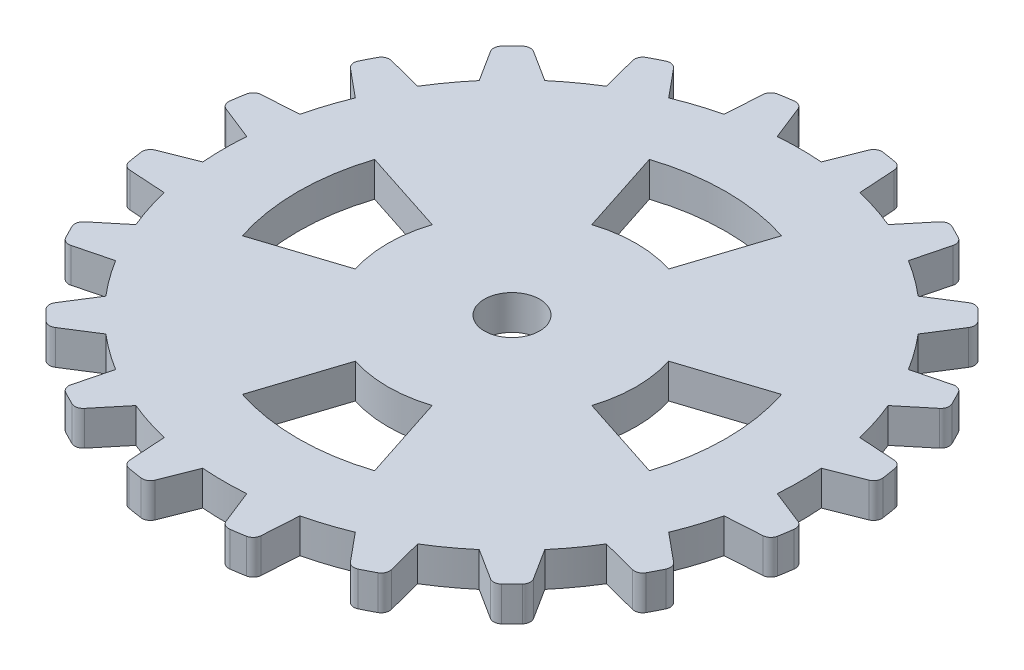
SolidWorks part; units mm, degrees
ref_plane "Front Plane" through (0, 0, 0) normal (0, 0, 1) x (1, 0, 0)
ref_plane "Top Plane" through (0, 0, 0) normal (0, 1, 0) x (1, 0, 0)
ref_plane "Right Plane" through (0, 0, 0) normal (1, 0, 0) x (0, 0, -1)
sketch "Sketch1" plane through (0, 0, 0) normal (0, 1, 0) x (1, 0, 0)
  line L0 (0, 0) -> (0, 28.8903) construction
  line L1 (-2.7439, 23.715) -> (0, 0)
  line L2 (2.7439, 23.715) -> (0, 0)
  line L3 (-2.7439, 23.715) -> (-1.5946, 20.8122)
  line L4 (2.7439, 23.715) -> (1.5946, 20.8122)
  line L5 (4.7187, 23.4022) -> (4.9148, 20.2864)
  line L6 (9.938, 21.7064) -> (7.9479, 19.3009)
  line L7 (11.7195, 20.7987) -> (10.943, 17.7748)
  line L8 (16.1592, 17.573) -> (13.5232, 15.9002)
  line L9 (17.573, 16.1592) -> (15.9002, 13.5232)
  line L10 (20.7987, 11.7195) -> (17.7748, 10.943)
  line L11 (21.7064, 9.938) -> (19.3009, 7.9479)
  line L12 (23.4022, 4.7187) -> (20.2864, 4.9148)
  line L13 (23.715, 2.7439) -> (20.8122, 1.5946)
  line L14 (23.715, -2.7439) -> (20.8122, -1.5946)
  line L15 (23.4022, -4.7187) -> (20.2864, -4.9148)
  line L16 (21.7064, -9.938) -> (19.3009, -7.9479)
  line L17 (20.7987, -11.7195) -> (17.7748, -10.943)
  line L18 (17.573, -16.1592) -> (15.9002, -13.5232)
  line L19 (16.1592, -17.573) -> (13.5232, -15.9002)
  line L20 (11.7195, -20.7987) -> (10.943, -17.7748)
  line L21 (9.938, -21.7064) -> (7.9479, -19.3009)
  line L22 (4.7187, -23.4022) -> (4.9148, -20.2864)
  line L23 (2.7439, -23.715) -> (1.5946, -20.8122)
  line L24 (-2.7439, -23.715) -> (-1.5946, -20.8122)
  line L25 (-4.7187, -23.4022) -> (-4.9148, -20.2864)
  line L26 (-9.938, -21.7064) -> (-7.9479, -19.3009)
  line L27 (-11.7195, -20.7987) -> (-10.943, -17.7748)
  line L28 (-16.1592, -17.573) -> (-13.5232, -15.9002)
  line L29 (-17.573, -16.1592) -> (-15.9002, -13.5232)
  line L30 (-20.7987, -11.7195) -> (-17.7748, -10.943)
  line L31 (-21.7064, -9.938) -> (-19.3009, -7.9479)
  line L32 (-23.4022, -4.7187) -> (-20.2864, -4.9148)
  line L33 (-23.715, -2.7439) -> (-20.8122, -1.5946)
  line L34 (-23.715, 2.7439) -> (-20.8122, 1.5946)
  line L35 (-23.4022, 4.7187) -> (-20.2864, 4.9148)
  line L36 (-21.7064, 9.938) -> (-19.3009, 7.9479)
  line L37 (-20.7987, 11.7195) -> (-17.7748, 10.943)
  line L38 (-17.573, 16.1592) -> (-15.9002, 13.5232)
  line L39 (-16.1592, 17.573) -> (-13.5232, 15.9002)
  line L40 (-11.7195, 20.7987) -> (-10.943, 17.7748)
  line L41 (-9.938, 21.7064) -> (-7.9479, 19.3009)
  line L42 (-4.7187, 23.4022) -> (-4.9148, 20.2864)
  line L43 (4.7898, 14.7414) -> (2.7812, 8.5595)
  line L44 (-4.7898, 14.7414) -> (-2.7812, 8.5595)
  line L45 (14.7414, -4.7898) -> (8.5595, -2.7812)
  line L46 (14.7414, 4.7898) -> (8.5595, 2.7812)
  line L47 (-4.7898, -14.7414) -> (-2.7812, -8.5595)
  line L48 (4.7898, -14.7414) -> (2.7812, -8.5595)
  line L49 (-14.7414, 4.7898) -> (-8.5595, 2.7812)
  line L50 (-14.7414, -4.7898) -> (-8.5595, -2.7812)
  circle A0 centre (0, 0) radius 23.8732
  circle A1 centre (0, 0) radius 20.8732
  circle A2 centre (0, 0) radius 9
  circle A3 centre (0, 0) radius 15.5
  point P4 (-2.7439, 23.715)
  point P7 (2.7439, 23.715)
  point P9 (-1.5946, 20.8122)
  point P13 (0, 20.8732)
  point P92 (0, 0)
  point P111 (0, 0)
  dimension "D1" = 47.7465
  dimension "D2" = 41.7465
  dimension "D8" = 18
  dimension "D9" = 31
  dimension "D3" = 13.2
  dimension "D4" = 6.6
  dimension "D5" = 15
  dimension "D6" = 15
  dimension "D10" = 18
  dimension "D11" = 18
  dimension "D7" = 20
  dimension "D12" = 4
extrude "Boss-Extrude1" add sketch "Sketch1" against normal blind 2.5 contours A1 L2 L1 | A1 L41 A0 L40 | A1 L1 A0 L42 | A1 L3 L1 | A1 L2 L4 | A1 L5 A0 L2 | A1 L7 A0 L6 | A1 L9 A0 L8 | A1 L11 A0 L10 | A1 L13 A0 L12 | L0 L2 A1 | L1 L0 A1 | A1 L15 A0 L14 | A1 L17 A0 L16 | A1 L19 A0 L18 | A1 L21 A0 L20 | A1 L23 A0 L22 | A1 L25 A0 L24 | A1 L27 A0 L26 | A1 L29 A0 L28 | A1 L31 A0 L30 | A1 L33 A0 L32 | A1 L39 A0 L38 | A1 L37 A0 L36 | A1 L35 A0 L34 | A3
fillet "Fillet1" radius 0.6 40 edges at (-9.938, -1.25, -21.7064) (-16.1592, -1.25, -17.573) (-23.715, -1.25, -2.7439) (-11.7195, -1.25, -20.7987) (-17.573, -1.25, -16.1592) (-20.7987, -1.25, -11.7195) (-21.7064, -1.25, -9.938) (-23.4022, -1.25, -4.7187) (-23.715, -1.25, 2.7439) (-21.7064, -1.25, 9.938) (-17.573, -1.25, 16.1592) (-23.4022, -1.25, 4.7187) (-20.7987, -1.25, 11.7195) (-16.1592, -1.25, 17.573) (-11.7195, -1.25, 20.7987) (-9.938, -1.25, 21.7064) (-4.7187, -1.25, 23.4022) (-2.7439, -1.25, 23.715) (2.7439, -1.25, 23.715) (4.7187, -1.25, 23.4022) (9.938, -1.25, 21.7064) (11.7195, -1.25, 20.7987) (16.1592, -1.25, 17.573) (17.573, -1.25, 16.1592) (20.7987, -1.25, 11.7195) (21.7064, -1.25, 9.938) (23.4022, -1.25, 4.7187) (23.715, -1.25, 2.7439) (23.715, -1.25, -2.7439) (23.4022, -1.25, -4.7187) (21.7064, -1.25, -9.938) (20.7987, -1.25, -11.7195) (17.573, -1.25, -16.1592) (16.1592, -1.25, -17.573) (11.7195, -1.25, -20.7987) (9.938, -1.25, -21.7064) (4.7187, -1.25, -23.4022) (2.7439, -1.25, -23.715) (-4.7187, -1.25, -23.4022) (-2.7439, -1.25, -23.715)
sketch "Sketch2" plane through (0, -2.5, 0) normal (0, -1, 0) x (1, 0, 0)
  line L0 (14.7414, -4.7898) -> (8.5595, -2.7812) construction
  line L1 (14.7414, 4.7898) -> (8.5595, 2.7812) construction
  line L2 (4.7898, 14.7414) -> (2.7812, 8.5595) construction
  line L3 (-4.7898, 14.7414) -> (-2.7812, 8.5595) construction
  line L4 (-14.7414, 4.7898) -> (-8.5595, 2.7812) construction
  line L5 (-14.7414, -4.7898) -> (-8.5595, -2.7812) construction
  line L6 (-4.7898, -14.7414) -> (-2.7812, -8.5595) construction
  line L7 (4.7898, -14.7414) -> (2.7812, -8.5595) construction
  line L8 (14.7414, -4.7898) -> (8.5595, -2.7812)
  line L9 (14.7414, 4.7898) -> (8.5595, 2.7812)
  line L10 (4.7898, 14.7414) -> (2.7812, 8.5595)
  line L11 (-4.7898, 14.7414) -> (-2.7812, 8.5595)
  line L12 (-14.7414, 4.7898) -> (-8.5595, 2.7812)
  line L13 (-14.7414, -4.7898) -> (-8.5595, -2.7812)
  line L14 (-4.7898, -14.7414) -> (-2.7812, -8.5595)
  line L15 (4.7898, -14.7414) -> (2.7812, -8.5595)
  circle A0 centre (0, 0) radius 9 construction
  circle A1 centre (0, 0) radius 15.5 construction
  circle A2 centre (0, 0) radius 9
  circle A3 centre (0, 0) radius 15.5
extrude "Cut-Extrude1" cut sketch "Sketch2" against normal through all contours L14 A3 L15 A2 | L8 A3 L9 A2 | L10 A3 L11 A2 | L12 A3 L13 A2
sketch "Sketch3" plane through (0, -2.5, 0) normal (0, -1, 0) x (1, 0, 0)
  circle A0 centre (0, 0) radius 2
  dimension "D1" = 4
extrude "Cut-Extrude2" cut sketch "Sketch3" against normal through all
